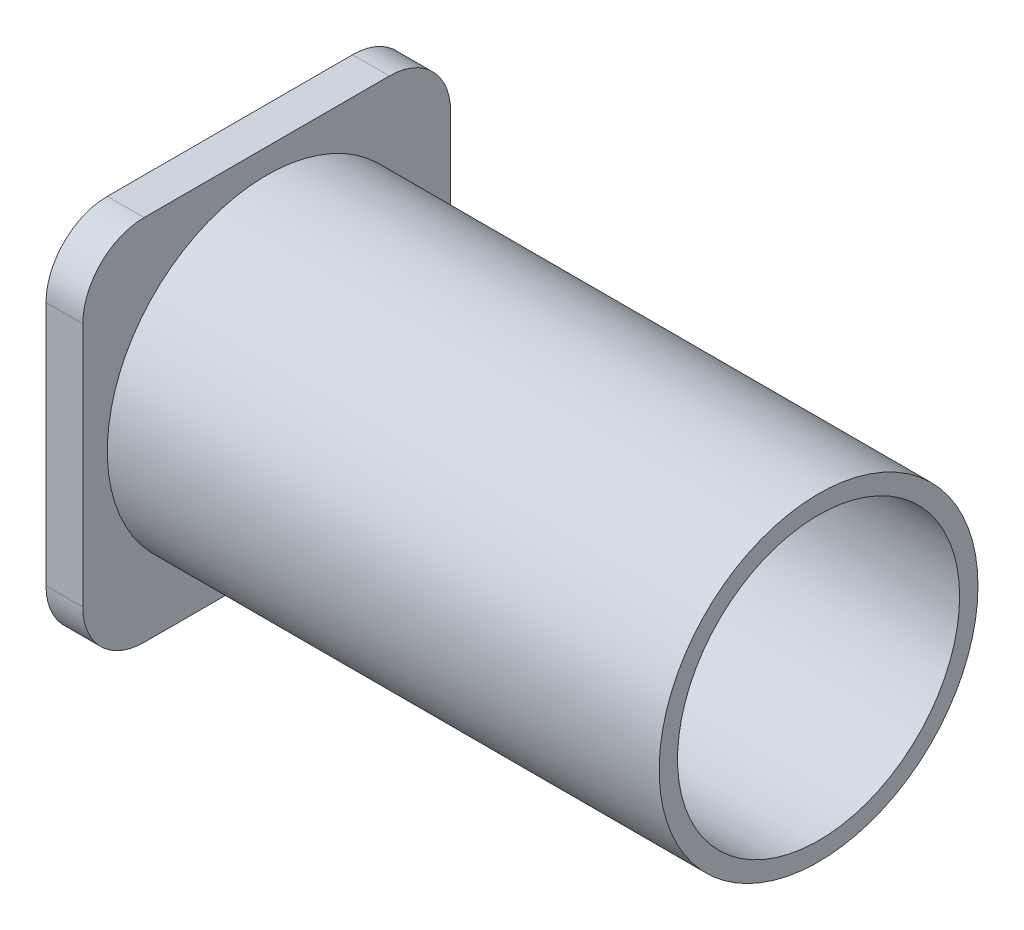
SolidWorks part; units mm, degrees
ref_plane "Front Plane" through (0, 0, 0) normal (0, 0, 1) x (1, 0, 0)
ref_plane "Top Plane" through (0, 0, 0) normal (0, 1, 0) x (1, 0, 0)
ref_plane "Right Plane" through (0, 0, 0) normal (1, 0, 0) x (0, 0, -1)
sketch "Sketch1" plane through (0, 0, 0) normal (1, 0, 0) x (0, 0, -1)
  circle A0 centre (0, 0) radius 13
  circle A1 centre (0, 0) radius 11.5
  dimension "D1" = 26
  dimension "D2" = 23
extrude "Boss-Extrude5" add sketch "Sketch1" along normal blind 45
sketch "Sketch5" plane through (0, 0, 0) normal (-1, 0, 0) x (0, 0, 1)
  line L1 (-10, 15) -> (10, 15)
  line L2 (-15, 10) -> (-15, -10)
  line L3 (-10, -15) -> (10, -15)
  line L4 (15, 10) -> (15, -10)
  line L5 (-15, 15) -> (15, -15) construction
  line L6 (-15, -15) -> (15, 15) construction
  arc A0 (-15, -10) -> (-10, -15) centre (-10, -10) ccw
  arc A1 (10, -15) -> (15, -10) centre (10, -10) ccw
  arc A2 (10, 15) -> (15, 10) centre (10, 10) cw
  arc A3 (-10, 15) -> (-15, 10) centre (-10, 10) ccw
  point P0 (0, 0)
  dimension "D3" = 5
  dimension "D1" = 30
  dimension "D2" = 30
extrude "Boss-Extrude7" add sketch "Sketch5" along normal blind 3
